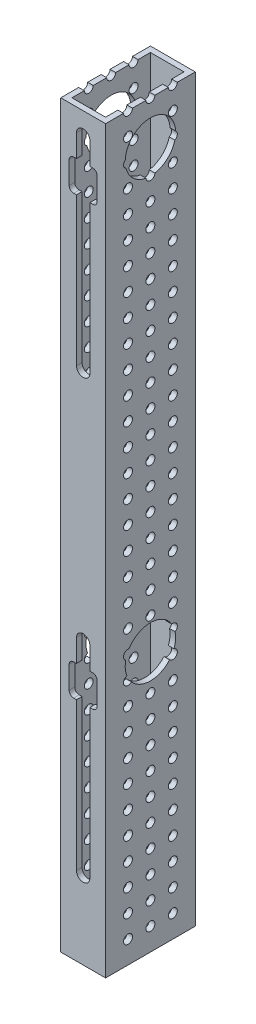
SolidWorks part; units mm, degrees
ref_plane "Front Plane" through (0, 0, 0) normal (0, 0, 1) x (1, 0, 0)
ref_plane "Top Plane" through (0, 0, 0) normal (0, 1, 0) x (1, 0, 0)
ref_plane "Right Plane" through (0, 0, 0) normal (1, 0, 0) x (0, 0, -1)
sketch "Sketch1" plane through (0, 0, 0) normal (0, 1, 0) x (1, 0, 0)
  line L1 (0, 0) -> (25.4, 0)
  line L2 (0, 0) -> (0, 50.8)
  line L3 (0, 50.8) -> (25.4, 50.8)
  line L4 (25.4, 0) -> (25.4, 50.8)
  dimension "D1" = 25.4
  dimension "D2" = 50.8
extrude "Boss-Extrude1" add sketch "Sketch1" along normal blind 419.1
shell "Shell1" thickness 3.175
sketch "Sketch2" plane through (0, 0, 0) normal (0, 0, 1) x (1, 0, 0)
  line L0 (12.7, 406.4) -> (12.7, 292.1) construction
  line L1 (16.51, 406.4) -> (16.51, 292.1)
  line L2 (8.89, 406.4) -> (8.89, 292.1)
  line L3 (0, 419.1) -> (25.4, 419.1) construction
  arc A0 (16.51, 406.4) -> (8.89, 406.4) centre (12.7, 406.4) ccw
  arc A1 (8.89, 292.1) -> (16.51, 292.1) centre (12.7, 292.1) ccw
  point P2 (12.7, 349.25)
  point P9 (12.7, 419.1)
  dimension "D1" = 7.62
  dimension "D2" = 114.3
  dimension "D3" = 12.7
extrude "Cut-Extrude1" cut sketch "Sketch2" against normal up to next (3.175 mm away)
sketch "Sketch3" plane through (25.4, 0, 0) normal (1, 0, 0) x (0, 0, -1)
  line L0 (3.175, 406.4) -> (0, 406.4) construction
  line L1 (3.175, 406.4) -> (0, 406.4) construction
  line L3 (0, 419.1) -> (50.8, 419.1) construction
  circle A0 centre (25.4, 394.97) radius 14.2875
  point P8 (25.4, 419.1)
  dimension "D1" = 28.575
  dimension "D2" = 11.43
extrude "Cut-Extrude2" cut sketch "Sketch3" against normal through all
sketch "Sketch4" plane through (0, 0, 0) normal (0, 0, 1) x (1, 0, 0)
  line L0 (16.51, 393.7) -> (18.0975, 393.7)
  line L1 (16.51, 406.4) -> (16.51, 292.1) construction
  line L2 (20.6375, 391.16) -> (20.6375, 378.46)
  line L3 (18.0975, 375.92) -> (16.51, 375.92)
  line L4 (12.7, 406.4) -> (12.7, 292.1) construction
  line L5 (12.7, 406.4) -> (12.7, 292.1) construction
  line L6 (7.3025, 375.92) -> (8.89, 375.92)
  line L7 (4.7625, 391.16) -> (4.7625, 378.46)
  line L8 (8.89, 393.7) -> (7.3025, 393.7)
  line L9 (8.89, 393.7) -> (16.51, 393.7)
  line L10 (8.89, 375.92) -> (16.51, 375.92)
  arc A0 (18.0975, 393.7) -> (20.6375, 391.16) centre (18.0975, 391.16) cw
  arc A1 (20.6375, 378.46) -> (18.0975, 375.92) centre (18.0975, 378.46) cw
  arc A2 (4.7625, 378.46) -> (7.3025, 375.92) centre (7.3025, 378.46) ccw
  arc A3 (7.3025, 393.7) -> (4.7625, 391.16) centre (7.3025, 391.16) ccw
  dimension "D1" = 2.54
  dimension "D5" = 2.54
  dimension "D2" = 1.5875
  dimension "D3" = 12.7
  dimension "D4" = 15.24
extrude "Cut-Extrude3" cut sketch "Sketch4" against normal up to next (3.175 mm away) contours A3 L7 A2 L6 L10 L3 A1 L2 A0 L0 L9 L8
pattern_linear "LPattern1" count 2 spacing 247.65 along (0, -1, 0) of "Cut-Extrude1", "Cut-Extrude2", "Cut-Extrude3"
sketch "Sketch6" plane through (0, 0, 0) normal (-1, 0, 0) x (0, 0, 1)
  line L0 (-50.8, 419.1) -> (-50.8, 0) construction
  line L1 (-50.8, 0) -> (0, 0) construction
  circle A0 centre (-38.1, 12.7) radius 2.54
  point P6 (0, 0)
  point P7 (-38.2365, 14.688)
  dimension "D1" = 5.08
  dimension "D2" = 12.7
  dimension "D3" = 12.7
extrude "Cut-Extrude4" cut sketch "Sketch6" against normal through all
pattern_linear "LPattern2" count 33 spacing 12.7 along (0, 1, 0) count 3 spacing 12.7 along (0, 0, 1) of "Cut-Extrude4"
